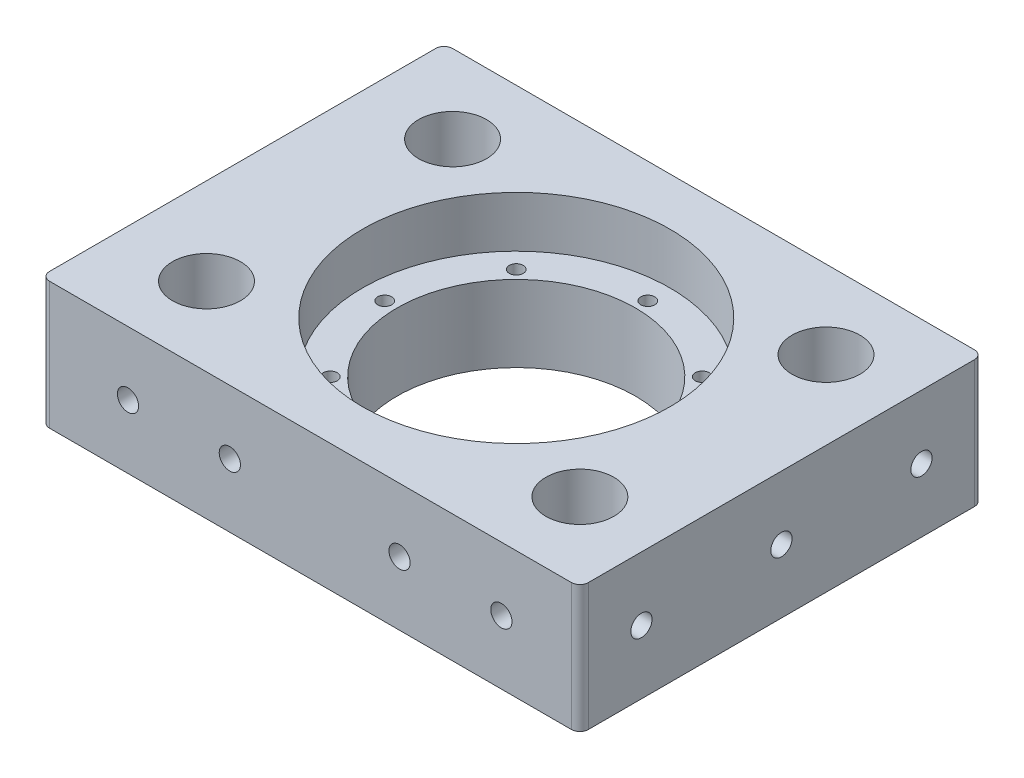
SolidWorks part; units mm, degrees
ref_plane "Front" through (0, 0, 0) normal (0, 0, 1) x (1, 0, 0)
ref_plane "Top" through (0, 0, 0) normal (0, 1, 0) x (1, 0, 0)
ref_plane "Right" through (0, 0, 0) normal (1, 0, 0) x (0, 0, -1)
sketch "Master Sketch" plane through (0, 0, 0) normal (0, 1, 0) x (1, 0, 0)
  line L0 (-158.5, 47.5) -> (-110.5, 0) construction
  line L1 (-62.5, -47.5) -> (62.5, -47.5) construction
  line L2 (-62.5, -47.5) -> (-62.5, 47.5) construction
  line L3 (-62.5, 47.5) -> (62.5, 47.5) construction
  line L4 (62.5, -47.5) -> (62.5, 47.5) construction
  line L5 (0, 47.5) -> (0, -47.5) construction
  line L6 (-62.5, 0) -> (62.5, 0) construction
  line L7 (-25.5, 10.5) -> (-62.5, 10.5) construction
  line L8 (-25.5, 10.5) -> (-25.5, 47.5) construction
  line L9 (-25.5, 47.5) -> (-62.5, 47.5) construction
  line L10 (-62.5, 10.5) -> (-62.5, 47.5) construction
  line L13 (25.5, 10.5) -> (62.5, 10.5) construction
  line L14 (25.5, 10.5) -> (25.5, 47.5) construction
  line L15 (25.5, 47.5) -> (62.5, 47.5) construction
  line L16 (62.5, 10.5) -> (62.5, 47.5) construction
  line L21 (25.5, -47.5) -> (62.5, -47.5) construction
  line L22 (62.5, -10.5) -> (62.5, -47.5) construction
  line L27 (-25.5, -47.5) -> (-62.5, -47.5) construction
  line L55 (-23.55, -23.55) -> (23.55, -23.55) construction
  line L56 (-23.55, -23.55) -> (-23.55, 23.55) construction
  line L57 (-23.55, 23.55) -> (23.55, 23.55) construction
  line L58 (23.55, -23.55) -> (23.55, 23.55) construction
  line L59 (0, 23.55) -> (0, -23.55) construction
  line L60 (-23.55, 0) -> (23.55, 0) construction
  line L61 (-62.5, 47.5) -> (-158.5, 47.5) construction
  line L62 (-62.5, 47.5) -> (-62.5, -47.5) construction
  line L63 (-62.5, -47.5) -> (-158.5, -47.5) construction
  line L64 (-158.5, 47.5) -> (-158.5, -47.5) construction
  line L65 (-110.5, 0) -> (-62.5, 47.5) construction
  line L66 (-110.5, 0) -> (-158.5, -47.5) construction
  line L67 (-62.5, -47.5) -> (-110.5, 0) construction
  circle A0 centre (0, 0) radius 12.5 construction
  circle A1 centre (44, 29) radius 8 construction
  circle A2 centre (44, -29) radius 8 construction
  circle A3 centre (-44, -29) radius 8 construction
  circle A4 centre (-44, 29) radius 8 construction
  circle A5 centre (-110.5, 0) radius 36.5125 construction
  circle A6 centre (0, 0) radius 28.6 construction
  circle A7 centre (-110.5, 0) radius 14.035 construction
  point P0 (0, 0)
  dimension "D3" = 25
  dimension "D4" = 16
  dimension "D9" = 73.025
  dimension "D10" = 88
  dimension "D11" = 28.07
  dimension "D6" = 58
  dimension "D12" = 29
  dimension "D13" = 44
  dimension "D1" = 125
  dimension "D2" = 95
  dimension "D5" = 37
  dimension "D7" = 47.1
  dimension "D8" = 96
sketch "Sketch2" plane through (0, 0, 0) normal (0, 1, 0) x (1, 0, 0)
  line L1 (-62.5, 47.5) -> (62.5, 47.5)
  line L2 (-62.5, 47.5) -> (-62.5, -47.5)
  line L3 (-62.5, -47.5) -> (62.5, -47.5)
  line L4 (62.5, 47.5) -> (62.5, -47.5)
  line L6 (-62.5, 0) -> (62.5, 0) construction
  line L8 (-158.5, 47.5) -> (-62.5, 47.5)
  line L9 (-158.5, 47.5) -> (-158.5, -47.5)
  line L10 (-158.5, -47.5) -> (-62.5, -47.5)
  line L11 (-62.5, 47.5) -> (-62.5, -47.5)
  circle A0 centre (-44, 29) radius 8
  circle A1 centre (-44, -29) radius 8
  circle A2 centre (44, -29) radius 8
  circle A3 centre (44, 29) radius 8
  circle A4 centre (-110.5, 0) radius 36.5125
  circle A5 centre (-44, 29) radius 8 construction
  circle A6 centre (-44, -29) radius 8 construction
  circle A7 centre (44, -29) radius 8 construction
  circle A8 centre (44, 29) radius 8 construction
  circle A9 centre (0, 0) radius 28.1
  dimension "D1" = 56.2
extrude "Boss-Extrude1" add sketch "Sketch2" along normal blind 30 contours L4 L1 L2 L3 A9 A3 A2 A1 A0
sketch "Sketch10" plane through (0, 30, 0) normal (0, 1, 0) x (1, 0, 0)
  circle A0 centre (0, 0) radius 36.25
  dimension "D1" = 72.5
extrude "Cut-Extrude3" cut sketch "Sketch10" against normal blind 12
hole_wizard "M4x0.7 Tapped Hole1" positions "Sketch12" profile "Sketch11" tap size "M4x0.7" standard "ANSI Metric" end condition through all
sketch "Sketch12" plane through (0, 18, 0) normal (0, 1, 0) x (1, 0, 0)
  line L0 (-62.5, 0) -> (62.5, 0) construction
  line L1 (0, 47.5) -> (0, -47.5) construction
  point P0 (0, 31)
  point P2 (31, 0)
  point P4 (0, -31)
  point P6 (-31, 0)
  dimension "D1" = 31
  dimension "D2" = 31
  dimension "D3" = 31
  dimension "D4" = 31
sketch "Sketch11" plane through (0, 18, -31) normal (1, 0, 0) x (0, 0, 1)
  line L0 (0, 0) -> (0, 18)
  line L1 (0, 18) -> (1.65, 18)
  line L2 (1.65, 18) -> (1.65, 0)
  line L5 (1.65, 0) -> (0, 0)
  line L11 (0, -6.35) -> (0, 107.95) construction
  dimension "Thru Tap Drill Dia." = 3.3
  dimension "Thru Tap Drill Depth" = 18
cosmetic thread "Hole Thread13" parameters "D1"=20, "D2"=4
cosmetic thread "Hole Thread14" parameters "D1"=20, "D2"=4
cosmetic thread "Hole Thread15" parameters "D1"=20, "D2"=4
cosmetic thread "Hole Thread16" parameters "D1"=20, "D2"=4
sketch "Sketch13" plane through (0, 0, -47.5) normal (0, 0, -1) x (-1, 0, 0)
  line L4 (-62.5, 0) -> (62.5, 0)
  line L5 (-62.5, 0) -> (62.5, 0)
  line L6 (62.5, 0) -> (62.5, 30)
  line L7 (-62.5, 30) -> (-62.5, 0)
  line L8 (62.5, 0) -> (62.5, 30)
  line L9 (62.5, 30) -> (-62.5, 30)
  line L10 (62.5, 30) -> (-62.5, 30)
  line L11 (-62.5, 30) -> (-62.5, 0)
  dimension "D1" = 0
hole_wizard "M6x1.0 Tapped Hole1" positions "Sketch15" profile "Sketch16" tap size "M6x1.0" standard "ANSI Metric"
sketch "Sketch15" plane through (0, 0, 47.5) normal (0, 0, 1) x (1, 0, 0)
  line L0 (0, 0) -> (-20, 15) construction
  line L1 (-20, 15) -> (0, 30) construction
  line L2 (-62.5, 30) -> (62.5, 30) construction
  line L3 (0, 30) -> (20, 15) construction
  line L4 (20, 15) -> (0, 0) construction
  line L6 (-62.5, 0) -> (62.5, 0) construction
  point P0 (-20, 15)
  point P2 (20, 15)
  dimension "D2" = 20
sketch "Sketch16" plane through (-20, 15, 47.5) normal (1, 0, 0) x (0, -1, 0)
  line L0 (0, 0) -> (0, 16.5022)
  line L1 (0, 16.5022) -> (2.5, 15)
  line L2 (2.5, 15) -> (2.5, 0)
  line L5 (2.5, 0) -> (0, 0)
  line L10 (0, 16.5022) -> (-2.5, 15) construction
  line L11 (0, -6.35) -> (0, 107.95) construction
  dimension "Tap Drill Dia." = 5
  dimension "Tap Drill Depth" = 15
  dimension "Drill Angle" = 118
cosmetic thread "Hole Thread17" parameters "D1"=12, "D2"=6
cosmetic thread "Hole Thread18" parameters "D1"=12, "D2"=6
sketch "Sketch19" plane through (-62.5, 0, 0) normal (-1, 0, 0) x (0, 0, 1)
  line L4 (-47.5, 0) -> (47.5, 0)
  line L5 (47.5, 0) -> (47.5, 30)
  line L6 (47.5, 30) -> (-47.5, 30)
  line L7 (-47.5, 30) -> (-47.5, 0)
  line L8 (-47.5, 0) -> (47.5, 0)
  line L9 (47.5, 0) -> (47.5, 30)
  line L10 (47.5, 30) -> (-47.5, 30)
  line L11 (-47.5, 30) -> (-47.5, 0)
  dimension "D1" = 0
extrude "Boss-Extrude3" add sketch "Sketch19" along normal blind 2
hole_wizard "M6x1.0 Tapped Hole2" positions "Sketch18" profile "Sketch17" tap size "M6x1.0" standard "ANSI Metric"
sketch "Sketch18" plane through (62.5, 0, 0) normal (-1, 0, 0) x (0, 0, 1)
  line L2 (-47.5, 15) -> (47.5, 15) construction
  line L3 (47.5, 0) -> (47.5, 30) construction
  line L4 (-47.5, 30) -> (-47.5, 0) construction
  line L5 (0, 18) -> (0, 30) construction
  point P0 (33, 15)
  point P2 (0, 15)
  point P4 (-33, 15)
  dimension "D1" = 33
  dimension "D2" = 33
cosmetic thread "Hole Thread20" parameters "D1"=8, "D2"=6
sketch "Sketch17" plane through (62.5, 15, 33) normal (0, 1, 0) x (0, 0, -1)
  line L0 (0, 0) -> (0, 12.5022)
  line L1 (0, 12.5022) -> (2.5, 11)
  line L2 (2.5, 11) -> (2.5, 0)
  line L5 (2.5, 0) -> (0, 0)
  line L10 (0, 12.5022) -> (-2.5, 11) construction
  line L11 (0, -6.35) -> (0, 107.95) construction
  dimension "Tap Drill Dia." = 5
  dimension "Tap Drill Depth" = 11
  dimension "Drill Angle" = 118
cosmetic thread "Hole Thread21" parameters "D1"=8, "D2"=6
cosmetic thread "Hole Thread22" parameters "D1"=8, "D2"=6
pattern_circular "CirPattern1" count 2 over 45 about axis through (0, 0, 0) along (0, 1, 0) of "M4x0.7 Tapped Hole1"
hole_wizard "M6x1.0 Tapped Hole5" positions "Sketch25" profile "Sketch24" tap size "M6x1.0" standard "ANSI Metric"
sketch "Sketch25" plane through (0, 0, 47.5) normal (0, 0, 1) x (1, 0, 0)
  line L0 (44, 30) -> (44, 0) construction
  line L1 (-44, 30) -> (-44, 0) construction
  point P0 (44, 15)
  point P6 (-44, 15)
sketch "Sketch24" plane through (44, 15, 47.5) normal (1, 0, 0) x (0, -1, 0)
  line L0 (0, 0) -> (0, 68.5)
  line L1 (0, 68.5) -> (2.5, 68.5)
  line L2 (2.5, 68.5) -> (2.5, 0)
  line L5 (2.5, 0) -> (0, 0)
  line L11 (0, -6.35) -> (0, 107.95) construction
  dimension "Thru Tap Drill Dia." = 5
  dimension "Thru Tap Drill Depth" = 68.5
cosmetic thread "Hole Thread26" parameters "D2"=6
cosmetic thread "Hole Thread27" parameters "D2"=6
fillet "Fillet1" radius 2 4 edges at (62.5, 15, 47.5) (-64.5, 15, 47.5) (-64.5, 15, -47.5) (62.5, 15, -47.5)
mirror "Mirror1" about plane through (0, 0, 0) normal (0, 0, 1) of "M6x1.0 Tapped Hole5"
